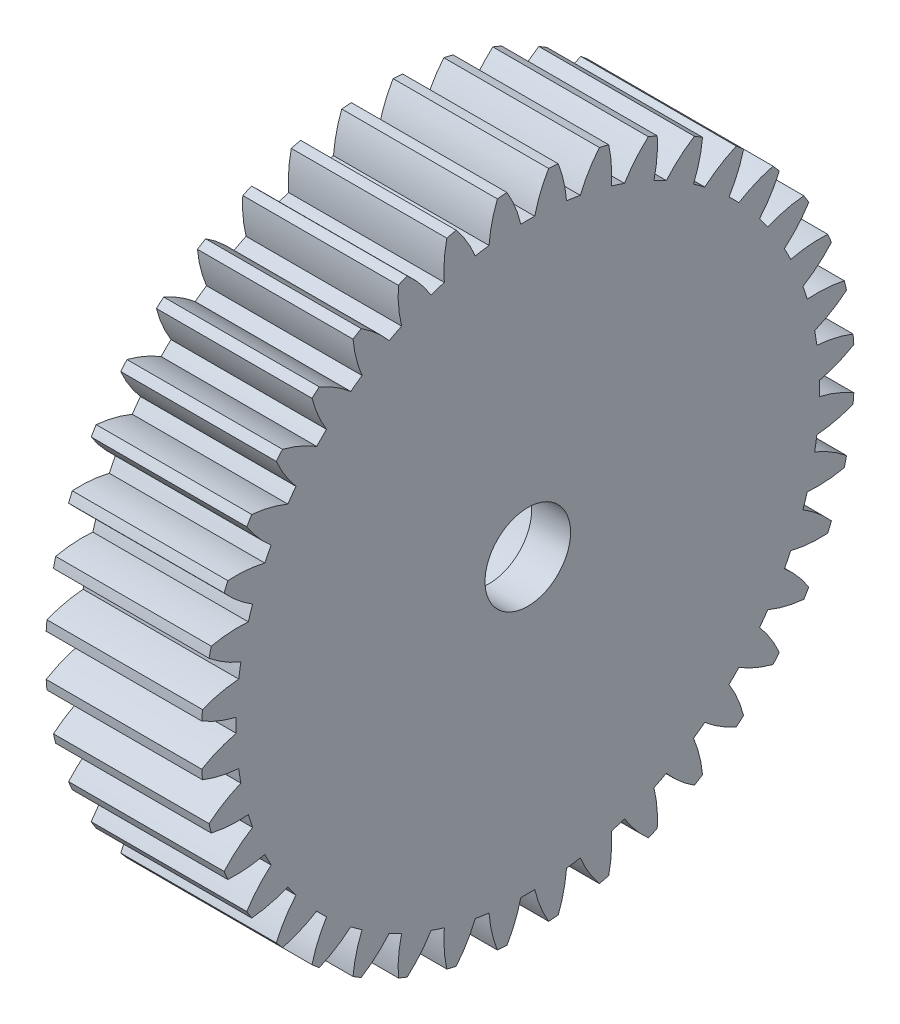
SolidWorks part; units mm, degrees
ref_plane "Front Plane" through (0, 0, 0) normal (0, 0, 1) x (1, 0, 0)
ref_plane "Top Plane" through (0, 0, 0) normal (0, 1, 0) x (1, 0, 0)
ref_plane "Right Plane" through (0, 0, 0) normal (1, 0, 0) x (0, 0, -1)
ref_plane "Plane1" through (-1.595, 0, 0) normal (1, 0, 0) x (0, 0, -1)
sketch "Sketch1" plane through (-1.595, 0, 0) normal (1, 0, 0) x (0, 0, -1)
  circle B0 centre (0, 0) radius 0.4
  arc B1 (-8.3829, 0.5357) -> (-7.4969, 0.179) centre (-6.7581, 3.2926) ccw
  arc B2 (-7.4969, 0.179) -> (-7.4969, -0.179) centre (0, 0) ccw
  arc B3 (-7.4969, -0.179) -> (-8.3829, -0.5357) centre (-6.7581, -3.2926) ccw
  arc B4 (-8.3829, -0.5357) -> (-8.3635, -0.7822) centre (0, 0) ccw
  arc B5 (-8.3635, -0.7822) -> (-7.4326, -0.996) centre (-7.19, 2.1948) ccw
  arc B6 (-7.4326, -0.996) -> (-7.3766, -1.3496) centre (0, 0) ccw
  arc B7 (-7.3766, -1.3496) -> (-8.1959, -1.8405) centre (-6.1599, -4.3092) ccw
  arc B8 (-8.1959, -1.8405) -> (-8.1382, -2.081) centre (0, 0) ccw
  arc B9 (-8.1382, -2.081) -> (-7.1853, -2.1464) centre (-7.4448, 1.043) ccw
  arc B10 (-7.1853, -2.1464) -> (-7.0746, -2.4869) centre (0, 0) ccw
  arc B11 (-7.0746, -2.4869) -> (-7.8071, -3.1) centre (-5.4099, -5.2198) ccw
  arc B12 (-7.8071, -3.1) -> (-7.7124, -3.3284) centre (0, 0) ccw
  arc B13 (-7.7124, -3.3284) -> (-6.761, -3.244) centre (-7.5163, -0.1344) ccw
  arc B14 (-6.761, -3.244) -> (-6.5985, -3.563) centre (0, 0) ccw
  arc B15 (-6.5985, -3.563) -> (-7.226, -4.2831) centre (-4.5268, -6.0018) ccw
  arc B16 (-7.226, -4.2831) -> (-7.0968, -4.4939) centre (0, 0) ccw
  arc B17 (-7.0968, -4.4939) -> (-6.1703, -4.2617) centre (-7.4028, -1.3086) ccw
  arc B18 (-6.1703, -4.2617) -> (-5.9599, -4.5514) centre (0, 0) ccw
  arc B19 (-5.9599, -4.5514) -> (-6.467, -5.3608) centre (-3.5321, -6.6361) ccw
  arc B20 (-6.467, -5.3608) -> (-6.3064, -5.5488) centre (0, 0) ccw
  arc B21 (-6.3064, -5.5488) -> (-5.4277, -5.1745) centre (-7.1069, -2.4505) ccw
  arc B22 (-5.4277, -5.1745) -> (-5.1745, -5.4277) centre (0, 0) ccw
  arc B23 (-5.1745, -5.4277) -> (-5.5488, -6.3064) centre (-2.4505, -7.1069) ccw
  arc B24 (-5.5488, -6.3064) -> (-5.3608, -6.467) centre (0, 0) ccw
  arc B25 (-5.3608, -6.467) -> (-4.5514, -5.9599) centre (-6.6361, -3.5321) ccw
  arc B26 (-4.5514, -5.9599) -> (-4.2617, -6.1703) centre (0, 0) ccw
  arc B27 (-4.2617, -6.1703) -> (-4.4939, -7.0968) centre (-1.3086, -7.4028) ccw
  arc B28 (-4.4939, -7.0968) -> (-4.2831, -7.226) centre (0, 0) ccw
  arc B29 (-4.2831, -7.226) -> (-3.563, -6.5985) centre (-6.0018, -4.5268) ccw
  arc B30 (-3.563, -6.5985) -> (-3.244, -6.761) centre (0, 0) ccw
  arc B31 (-3.244, -6.761) -> (-3.3284, -7.7124) centre (-0.1344, -7.5163) ccw
  arc B32 (-3.3284, -7.7124) -> (-3.1, -7.8071) centre (0, 0) ccw
  arc B33 (-3.1, -7.8071) -> (-2.4869, -7.0746) centre (-5.2198, -5.4099) ccw
  arc B34 (-2.4869, -7.0746) -> (-2.1464, -7.1853) centre (0, 0) ccw
  arc B35 (-2.1464, -7.1853) -> (-2.081, -8.1382) centre (1.043, -7.4448) ccw
  arc B36 (-2.081, -8.1382) -> (-1.8405, -8.1959) centre (0, 0) ccw
  arc B37 (-1.8405, -8.1959) -> (-1.3496, -7.3766) centre (-4.3092, -6.1599) ccw
  arc B38 (-1.3496, -7.3766) -> (-0.996, -7.4326) centre (0, 0) ccw
  arc B39 (-0.996, -7.4326) -> (-0.7822, -8.3635) centre (2.1948, -7.19) ccw
  arc B40 (-0.7822, -8.3635) -> (-0.5357, -8.3829) centre (0, 0) ccw
  arc B41 (-0.5357, -8.3829) -> (-0.179, -7.4969) centre (-3.2926, -6.7581) ccw
  arc B42 (-0.179, -7.4969) -> (0.179, -7.4969) centre (0, 0) ccw
  arc B43 (0.179, -7.4969) -> (0.5357, -8.3829) centre (3.2926, -6.7581) ccw
  arc B44 (0.5357, -8.3829) -> (0.7822, -8.3635) centre (0, 0) ccw
  arc B45 (0.7822, -8.3635) -> (0.996, -7.4326) centre (-2.1948, -7.19) ccw
  arc B46 (0.996, -7.4326) -> (1.3496, -7.3766) centre (0, 0) ccw
  arc B47 (1.3496, -7.3766) -> (1.8405, -8.1959) centre (4.3092, -6.1599) ccw
  arc B48 (1.8405, -8.1959) -> (2.081, -8.1382) centre (0, 0) ccw
  arc B49 (2.081, -8.1382) -> (2.1464, -7.1853) centre (-1.043, -7.4448) ccw
  arc B50 (2.1464, -7.1853) -> (2.4869, -7.0746) centre (0, 0) ccw
  arc B51 (2.4869, -7.0746) -> (3.1, -7.8071) centre (5.2198, -5.4099) ccw
  arc B52 (3.1, -7.8071) -> (3.3284, -7.7124) centre (0, 0) ccw
  arc B53 (3.3284, -7.7124) -> (3.244, -6.761) centre (0.1344, -7.5163) ccw
  arc B54 (3.244, -6.761) -> (3.563, -6.5985) centre (0, 0) ccw
  arc B55 (3.563, -6.5985) -> (4.2831, -7.226) centre (6.0018, -4.5268) ccw
  arc B56 (4.2831, -7.226) -> (4.4939, -7.0968) centre (0, 0) ccw
  arc B57 (4.4939, -7.0968) -> (4.2617, -6.1703) centre (1.3086, -7.4028) ccw
  arc B58 (4.2617, -6.1703) -> (4.5514, -5.9599) centre (0, 0) ccw
  arc B59 (4.5514, -5.9599) -> (5.3608, -6.467) centre (6.6361, -3.5321) ccw
  arc B60 (5.3608, -6.467) -> (5.5488, -6.3064) centre (0, 0) ccw
  arc B61 (5.5488, -6.3064) -> (5.1745, -5.4277) centre (2.4505, -7.1069) ccw
  arc B62 (5.1745, -5.4277) -> (5.4277, -5.1745) centre (0, 0) ccw
  arc B63 (5.4277, -5.1745) -> (6.3064, -5.5488) centre (7.1069, -2.4505) ccw
  arc B64 (6.3064, -5.5488) -> (6.467, -5.3608) centre (0, 0) ccw
  arc B65 (6.467, -5.3608) -> (5.9599, -4.5514) centre (3.5321, -6.6361) ccw
  arc B66 (5.9599, -4.5514) -> (6.1703, -4.2617) centre (0, 0) ccw
  arc B67 (6.1703, -4.2617) -> (7.0968, -4.4939) centre (7.4028, -1.3086) ccw
  arc B68 (7.0968, -4.4939) -> (7.226, -4.2831) centre (0, 0) ccw
  arc B69 (7.226, -4.2831) -> (6.5985, -3.563) centre (4.5268, -6.0018) ccw
  arc B70 (6.5985, -3.563) -> (6.761, -3.244) centre (0, 0) ccw
  arc B71 (6.761, -3.244) -> (7.7124, -3.3284) centre (7.5163, -0.1344) ccw
  arc B72 (7.7124, -3.3284) -> (7.8071, -3.1) centre (0, 0) ccw
  arc B73 (7.8071, -3.1) -> (7.0746, -2.4869) centre (5.4099, -5.2198) ccw
  arc B74 (7.0746, -2.4869) -> (7.1853, -2.1464) centre (0, 0) ccw
  arc B75 (7.1853, -2.1464) -> (8.1382, -2.081) centre (7.4448, 1.043) ccw
  arc B76 (8.1382, -2.081) -> (8.1959, -1.8405) centre (0, 0) ccw
  arc B77 (8.1959, -1.8405) -> (7.3766, -1.3496) centre (6.1599, -4.3092) ccw
  arc B78 (7.3766, -1.3496) -> (7.4326, -0.996) centre (0, 0) ccw
  arc B79 (7.4326, -0.996) -> (8.3635, -0.7822) centre (7.19, 2.1948) ccw
  arc B80 (8.3635, -0.7822) -> (8.3829, -0.5357) centre (0, 0) ccw
  arc B81 (8.3829, -0.5357) -> (7.4969, -0.179) centre (6.7581, -3.2926) ccw
  arc B82 (7.4969, -0.179) -> (7.4969, 0.179) centre (0, 0) ccw
  arc B83 (7.4969, 0.179) -> (8.3829, 0.5357) centre (6.7581, 3.2926) ccw
  arc B84 (8.3829, 0.5357) -> (8.3635, 0.7822) centre (0, 0) ccw
  arc B85 (8.3635, 0.7822) -> (7.4326, 0.996) centre (7.19, -2.1948) ccw
  arc B86 (7.4326, 0.996) -> (7.3766, 1.3496) centre (0, 0) ccw
  arc B87 (7.3766, 1.3496) -> (8.1959, 1.8405) centre (6.1599, 4.3092) ccw
  arc B88 (8.1959, 1.8405) -> (8.1382, 2.081) centre (0, 0) ccw
  arc B89 (8.1382, 2.081) -> (7.1853, 2.1464) centre (7.4448, -1.043) ccw
  arc B90 (7.1853, 2.1464) -> (7.0746, 2.4869) centre (0, 0) ccw
  arc B91 (7.0746, 2.4869) -> (7.8071, 3.1) centre (5.4099, 5.2198) ccw
  arc B92 (7.8071, 3.1) -> (7.7124, 3.3284) centre (0, 0) ccw
  arc B93 (7.7124, 3.3284) -> (6.761, 3.244) centre (7.5163, 0.1344) ccw
  arc B94 (6.761, 3.244) -> (6.5985, 3.563) centre (0, 0) ccw
  arc B95 (6.5985, 3.563) -> (7.226, 4.2831) centre (4.5268, 6.0018) ccw
  arc B96 (7.226, 4.2831) -> (7.0968, 4.4939) centre (0, 0) ccw
  arc B97 (7.0968, 4.4939) -> (6.1703, 4.2617) centre (7.4028, 1.3086) ccw
  arc B98 (6.1703, 4.2617) -> (5.9599, 4.5514) centre (0, 0) ccw
  arc B99 (5.9599, 4.5514) -> (6.467, 5.3608) centre (3.5321, 6.6361) ccw
  arc B100 (6.467, 5.3608) -> (6.3064, 5.5488) centre (0, 0) ccw
  arc B101 (6.3064, 5.5488) -> (5.4277, 5.1745) centre (7.1069, 2.4505) ccw
  arc B102 (5.4277, 5.1745) -> (5.1745, 5.4277) centre (0, 0) ccw
  arc B103 (5.1745, 5.4277) -> (5.5488, 6.3064) centre (2.4505, 7.1069) ccw
  arc B104 (5.5488, 6.3064) -> (5.3608, 6.467) centre (0, 0) ccw
  arc B105 (5.3608, 6.467) -> (4.5514, 5.9599) centre (6.6361, 3.5321) ccw
  arc B106 (4.5514, 5.9599) -> (4.2617, 6.1703) centre (0, 0) ccw
  arc B107 (4.2617, 6.1703) -> (4.4939, 7.0968) centre (1.3086, 7.4028) ccw
  arc B108 (4.4939, 7.0968) -> (4.2831, 7.226) centre (0, 0) ccw
  arc B109 (4.2831, 7.226) -> (3.563, 6.5985) centre (6.0018, 4.5268) ccw
  arc B110 (3.563, 6.5985) -> (3.244, 6.761) centre (0, 0) ccw
  arc B111 (3.244, 6.761) -> (3.3284, 7.7124) centre (0.1344, 7.5163) ccw
  arc B112 (3.3284, 7.7124) -> (3.1, 7.8071) centre (0, 0) ccw
  arc B113 (3.1, 7.8071) -> (2.4869, 7.0746) centre (5.2198, 5.4099) ccw
  arc B114 (2.4869, 7.0746) -> (2.1464, 7.1853) centre (0, 0) ccw
  arc B115 (2.1464, 7.1853) -> (2.081, 8.1382) centre (-1.043, 7.4448) ccw
  arc B116 (2.081, 8.1382) -> (1.8405, 8.1959) centre (0, 0) ccw
  arc B117 (1.8405, 8.1959) -> (1.3496, 7.3766) centre (4.3092, 6.1599) ccw
  arc B118 (1.3496, 7.3766) -> (0.996, 7.4326) centre (0, 0) ccw
  arc B119 (0.996, 7.4326) -> (0.7822, 8.3635) centre (-2.1948, 7.19) ccw
  arc B120 (0.7822, 8.3635) -> (0.5357, 8.3829) centre (0, 0) ccw
  arc B121 (0.5357, 8.3829) -> (0.179, 7.4969) centre (3.2926, 6.7581) ccw
  arc B122 (0.179, 7.4969) -> (-0.179, 7.4969) centre (0, 0) ccw
  arc B123 (-0.179, 7.4969) -> (-0.5357, 8.3829) centre (-3.2926, 6.7581) ccw
  arc B124 (-0.5357, 8.3829) -> (-0.7822, 8.3635) centre (0, 0) ccw
  arc B125 (-0.7822, 8.3635) -> (-0.996, 7.4326) centre (2.1948, 7.19) ccw
  arc B126 (-0.996, 7.4326) -> (-1.3496, 7.3766) centre (0, 0) ccw
  arc B127 (-1.3496, 7.3766) -> (-1.8405, 8.1959) centre (-4.3092, 6.1599) ccw
  arc B128 (-1.8405, 8.1959) -> (-2.081, 8.1382) centre (0, 0) ccw
  arc B129 (-2.081, 8.1382) -> (-2.1464, 7.1853) centre (1.043, 7.4448) ccw
  arc B130 (-2.1464, 7.1853) -> (-2.4869, 7.0746) centre (0, 0) ccw
  arc B131 (-2.4869, 7.0746) -> (-3.1, 7.8071) centre (-5.2198, 5.4099) ccw
  arc B132 (-3.1, 7.8071) -> (-3.3284, 7.7124) centre (0, 0) ccw
  arc B133 (-3.3284, 7.7124) -> (-3.244, 6.761) centre (-0.1344, 7.5163) ccw
  arc B134 (-3.244, 6.761) -> (-3.563, 6.5985) centre (0, 0) ccw
  arc B135 (-3.563, 6.5985) -> (-4.2831, 7.226) centre (-6.0018, 4.5268) ccw
  arc B136 (-4.2831, 7.226) -> (-4.4939, 7.0968) centre (0, 0) ccw
  arc B137 (-4.4939, 7.0968) -> (-4.2617, 6.1703) centre (-1.3086, 7.4028) ccw
  arc B138 (-4.2617, 6.1703) -> (-4.5514, 5.9599) centre (0, 0) ccw
  arc B139 (-4.5514, 5.9599) -> (-5.3608, 6.467) centre (-6.6361, 3.5321) ccw
  arc B140 (-5.3608, 6.467) -> (-5.5488, 6.3064) centre (0, 0) ccw
  arc B141 (-5.5488, 6.3064) -> (-5.1745, 5.4277) centre (-2.4505, 7.1069) ccw
  arc B142 (-5.1745, 5.4277) -> (-5.4277, 5.1745) centre (0, 0) ccw
  arc B143 (-5.4277, 5.1745) -> (-6.3064, 5.5488) centre (-7.1069, 2.4505) ccw
  arc B144 (-6.3064, 5.5488) -> (-6.467, 5.3608) centre (0, 0) ccw
  arc B145 (-6.467, 5.3608) -> (-5.9599, 4.5514) centre (-3.5321, 6.6361) ccw
  arc B146 (-5.9599, 4.5514) -> (-6.1703, 4.2617) centre (0, 0) ccw
  arc B147 (-6.1703, 4.2617) -> (-7.0968, 4.4939) centre (-7.4028, 1.3086) ccw
  arc B148 (-7.0968, 4.4939) -> (-7.226, 4.2831) centre (0, 0) ccw
  arc B149 (-7.226, 4.2831) -> (-6.5985, 3.563) centre (-4.5268, 6.0018) ccw
  arc B150 (-6.5985, 3.563) -> (-6.761, 3.244) centre (0, 0) ccw
  arc B151 (-6.761, 3.244) -> (-7.7124, 3.3284) centre (-7.5163, 0.1344) ccw
  arc B152 (-7.7124, 3.3284) -> (-7.8071, 3.1) centre (0, 0) ccw
  arc B153 (-7.8071, 3.1) -> (-7.0746, 2.4869) centre (-5.4099, 5.2198) ccw
  arc B154 (-7.0746, 2.4869) -> (-7.1853, 2.1464) centre (0, 0) ccw
  arc B155 (-7.1853, 2.1464) -> (-8.1382, 2.081) centre (-7.4448, -1.043) ccw
  arc B156 (-8.1382, 2.081) -> (-8.1959, 1.8405) centre (0, 0) ccw
  arc B157 (-8.1959, 1.8405) -> (-7.3766, 1.3496) centre (-6.1599, 4.3092) ccw
  arc B158 (-7.3766, 1.3496) -> (-7.4326, 0.996) centre (0, 0) ccw
  arc B159 (-7.4326, 0.996) -> (-8.3635, 0.7822) centre (-7.19, -2.1948) ccw
  arc B160 (-8.3635, 0.7822) -> (-8.3829, 0.5357) centre (0, 0) ccw
sketch_block_instance "Block2-1"
sketch_block "Block2"
extrude "Boss-Extrude1" add sketch "Sketch1" against normal blind 3
sketch "Sketch4" plane through (-1.595, 0, 0) normal (1, 0, 0) x (0, 0, -1)
  circle A0 centre (0, 0) radius 2.55
  dimension "D1" = 5.1
extrude "Cut-Extrude2" cut sketch "Sketch4" against normal through all
sketch "Sketch5" plane through (-1.595, 0, 0) normal (1, 0, 0) x (0, 0, -1)
  arc A160 (-8.3635, 0.7822) -> (-8.3829, 0.5357) centre (0, 0) ccw
  arc A161 (-8.3829, 0.5357) -> (-7.4969, 0.179) centre (-6.7581, 3.2926) ccw
  arc A162 (-7.4969, 0.179) -> (-7.4969, -0.179) centre (0, 0) ccw
  arc A163 (-7.4969, -0.179) -> (-8.3829, -0.5357) centre (-6.7581, -3.2926) ccw
  arc A164 (-8.3829, -0.5357) -> (-8.3635, -0.7822) centre (0, 0) ccw
  arc A165 (-8.3635, -0.7822) -> (-7.4326, -0.996) centre (-7.19, 2.1948) ccw
  arc A166 (-7.4326, -0.996) -> (-7.3766, -1.3496) centre (0, 0) ccw
  arc A167 (-7.3766, -1.3496) -> (-8.1959, -1.8405) centre (-6.1599, -4.3092) ccw
  arc A168 (-8.1959, -1.8405) -> (-8.1382, -2.081) centre (0, 0) ccw
  arc A169 (-8.1382, -2.081) -> (-7.1853, -2.1464) centre (-7.4448, 1.043) ccw
  arc A170 (-7.1853, -2.1464) -> (-7.0746, -2.4869) centre (0, 0) ccw
  arc A171 (-7.0746, -2.4869) -> (-7.8071, -3.1) centre (-5.4099, -5.2198) ccw
  arc A172 (-7.8071, -3.1) -> (-7.7124, -3.3284) centre (0, 0) ccw
  arc A173 (-7.7124, -3.3284) -> (-6.761, -3.244) centre (-7.5163, -0.1344) ccw
  arc A174 (-6.761, -3.244) -> (-6.5985, -3.563) centre (0, 0) ccw
  arc A175 (-6.5985, -3.563) -> (-7.226, -4.2831) centre (-4.5268, -6.0018) ccw
  arc A176 (-7.226, -4.2831) -> (-7.0968, -4.4939) centre (0, 0) ccw
  arc A177 (-7.0968, -4.4939) -> (-6.1703, -4.2617) centre (-7.4028, -1.3086) ccw
  arc A178 (-6.1703, -4.2617) -> (-5.9599, -4.5514) centre (0, 0) ccw
  arc A179 (-5.9599, -4.5514) -> (-6.467, -5.3608) centre (-3.5321, -6.6361) ccw
  arc A180 (-6.467, -5.3608) -> (-6.3064, -5.5488) centre (0, 0) ccw
  arc A181 (-6.3064, -5.5488) -> (-5.4277, -5.1745) centre (-7.1069, -2.4505) ccw
  arc A182 (-5.4277, -5.1745) -> (-5.1745, -5.4277) centre (0, 0) ccw
  arc A183 (-5.1745, -5.4277) -> (-5.5488, -6.3064) centre (-2.4505, -7.1069) ccw
  arc A184 (-5.5488, -6.3064) -> (-5.3608, -6.467) centre (0, 0) ccw
  arc A185 (-5.3608, -6.467) -> (-4.5514, -5.9599) centre (-6.6361, -3.5321) ccw
  arc A186 (-4.5514, -5.9599) -> (-4.2617, -6.1703) centre (0, 0) ccw
  arc A187 (-4.2617, -6.1703) -> (-4.4939, -7.0968) centre (-1.3086, -7.4028) ccw
  arc A188 (-4.4939, -7.0968) -> (-4.2831, -7.226) centre (0, 0) ccw
  arc A189 (-4.2831, -7.226) -> (-3.563, -6.5985) centre (-6.0018, -4.5268) ccw
  arc A190 (-3.563, -6.5985) -> (-3.244, -6.761) centre (0, 0) ccw
  arc A191 (-3.244, -6.761) -> (-3.3284, -7.7124) centre (-0.1344, -7.5163) ccw
  arc A192 (-3.3284, -7.7124) -> (-3.1, -7.8071) centre (0, 0) ccw
  arc A193 (-3.1, -7.8071) -> (-2.4869, -7.0746) centre (-5.2198, -5.4099) ccw
  arc A194 (-2.4869, -7.0746) -> (-2.1464, -7.1853) centre (0, 0) ccw
  arc A195 (-2.1464, -7.1853) -> (-2.081, -8.1382) centre (1.043, -7.4448) ccw
  arc A196 (-2.081, -8.1382) -> (-1.8405, -8.1959) centre (0, 0) ccw
  arc A197 (-1.8405, -8.1959) -> (-1.3496, -7.3766) centre (-4.3092, -6.1599) ccw
  arc A198 (-1.3496, -7.3766) -> (-0.996, -7.4326) centre (0, 0) ccw
  arc A199 (-0.996, -7.4326) -> (-0.7822, -8.3635) centre (2.1948, -7.19) ccw
  arc A200 (-0.7822, -8.3635) -> (-0.5357, -8.3829) centre (0, 0) ccw
  arc A201 (-0.5357, -8.3829) -> (-0.179, -7.4969) centre (-3.2926, -6.7581) ccw
  arc A202 (-0.179, -7.4969) -> (0.179, -7.4969) centre (0, 0) ccw
  arc A203 (0.179, -7.4969) -> (0.5357, -8.3829) centre (3.2926, -6.7581) ccw
  arc A204 (0.5357, -8.3829) -> (0.7822, -8.3635) centre (0, 0) ccw
  arc A205 (0.7822, -8.3635) -> (0.996, -7.4326) centre (-2.1948, -7.19) ccw
  arc A206 (0.996, -7.4326) -> (1.3496, -7.3766) centre (0, 0) ccw
  arc A207 (1.3496, -7.3766) -> (1.8405, -8.1959) centre (4.3092, -6.1599) ccw
  arc A208 (1.8405, -8.1959) -> (2.081, -8.1382) centre (0, 0) ccw
  arc A209 (2.081, -8.1382) -> (2.1464, -7.1853) centre (-1.043, -7.4448) ccw
  arc A210 (2.1464, -7.1853) -> (2.4869, -7.0746) centre (0, 0) ccw
  arc A211 (2.4869, -7.0746) -> (3.1, -7.8071) centre (5.2198, -5.4099) ccw
  arc A212 (3.1, -7.8071) -> (3.3284, -7.7124) centre (0, 0) ccw
  arc A213 (3.3284, -7.7124) -> (3.244, -6.761) centre (0.1344, -7.5163) ccw
  arc A214 (3.244, -6.761) -> (3.563, -6.5985) centre (0, 0) ccw
  arc A215 (3.563, -6.5985) -> (4.2831, -7.226) centre (6.0018, -4.5268) ccw
  arc A216 (4.2831, -7.226) -> (4.4939, -7.0968) centre (0, 0) ccw
  arc A217 (4.4939, -7.0968) -> (4.2617, -6.1703) centre (1.3086, -7.4028) ccw
  arc A218 (4.2617, -6.1703) -> (4.5514, -5.9599) centre (0, 0) ccw
  arc A219 (4.5514, -5.9599) -> (5.3608, -6.467) centre (6.6361, -3.5321) ccw
  arc A220 (5.3608, -6.467) -> (5.5488, -6.3064) centre (0, 0) ccw
  arc A221 (5.5488, -6.3064) -> (5.1745, -5.4277) centre (2.4505, -7.1069) ccw
  arc A222 (5.1745, -5.4277) -> (5.4277, -5.1745) centre (0, 0) ccw
  arc A223 (5.4277, -5.1745) -> (6.3064, -5.5488) centre (7.1069, -2.4505) ccw
  arc A224 (6.3064, -5.5488) -> (6.467, -5.3608) centre (0, 0) ccw
  arc A225 (6.467, -5.3608) -> (5.9599, -4.5514) centre (3.5321, -6.6361) ccw
  arc A226 (5.9599, -4.5514) -> (6.1703, -4.2617) centre (0, 0) ccw
  arc A227 (6.1703, -4.2617) -> (7.0968, -4.4939) centre (7.4028, -1.3086) ccw
  arc A228 (7.0968, -4.4939) -> (7.226, -4.2831) centre (0, 0) ccw
  arc A229 (7.226, -4.2831) -> (6.5985, -3.563) centre (4.5268, -6.0018) ccw
  arc A230 (6.5985, -3.563) -> (6.761, -3.244) centre (0, 0) ccw
  arc A231 (6.761, -3.244) -> (7.7124, -3.3284) centre (7.5163, -0.1344) ccw
  arc A232 (7.7124, -3.3284) -> (7.8071, -3.1) centre (0, 0) ccw
  arc A233 (7.8071, -3.1) -> (7.0746, -2.4869) centre (5.4099, -5.2198) ccw
  arc A234 (7.0746, -2.4869) -> (7.1853, -2.1464) centre (0, 0) ccw
  arc A235 (7.1853, -2.1464) -> (8.1382, -2.081) centre (7.4448, 1.043) ccw
  arc A236 (8.1382, -2.081) -> (8.1959, -1.8405) centre (0, 0) ccw
  arc A237 (8.1959, -1.8405) -> (7.3766, -1.3496) centre (6.1599, -4.3092) ccw
  arc A238 (7.3766, -1.3496) -> (7.4326, -0.996) centre (0, 0) ccw
  arc A239 (7.4326, -0.996) -> (8.3635, -0.7822) centre (7.19, 2.1948) ccw
  arc A240 (8.3635, -0.7822) -> (8.3829, -0.5357) centre (0, 0) ccw
  arc A241 (8.3829, -0.5357) -> (7.4969, -0.179) centre (6.7581, -3.2926) ccw
  arc A242 (7.4969, -0.179) -> (7.4969, 0.179) centre (0, 0) ccw
  arc A243 (7.4969, 0.179) -> (8.3829, 0.5357) centre (6.7581, 3.2926) ccw
  arc A244 (8.3829, 0.5357) -> (8.3635, 0.7822) centre (0, 0) ccw
  arc A245 (8.3635, 0.7822) -> (7.4326, 0.996) centre (7.19, -2.1948) ccw
  arc A246 (7.4326, 0.996) -> (7.3766, 1.3496) centre (0, 0) ccw
  arc A247 (7.3766, 1.3496) -> (8.1959, 1.8405) centre (6.1599, 4.3092) ccw
  arc A248 (8.1959, 1.8405) -> (8.1382, 2.081) centre (0, 0) ccw
  arc A249 (8.1382, 2.081) -> (7.1853, 2.1464) centre (7.4448, -1.043) ccw
  arc A250 (7.1853, 2.1464) -> (7.0746, 2.4869) centre (0, 0) ccw
  arc A251 (7.0746, 2.4869) -> (7.8071, 3.1) centre (5.4099, 5.2198) ccw
  arc A252 (7.8071, 3.1) -> (7.7124, 3.3284) centre (0, 0) ccw
  arc A253 (7.7124, 3.3284) -> (6.761, 3.244) centre (7.5163, 0.1344) ccw
  arc A254 (6.761, 3.244) -> (6.5985, 3.563) centre (0, 0) ccw
  arc A255 (6.5985, 3.563) -> (7.226, 4.2831) centre (4.5268, 6.0018) ccw
  arc A256 (7.226, 4.2831) -> (7.0968, 4.4939) centre (0, 0) ccw
  arc A257 (7.0968, 4.4939) -> (6.1703, 4.2617) centre (7.4028, 1.3086) ccw
  arc A258 (6.1703, 4.2617) -> (5.9599, 4.5514) centre (0, 0) ccw
  arc A259 (5.9599, 4.5514) -> (6.467, 5.3608) centre (3.5321, 6.6361) ccw
  arc A260 (6.467, 5.3608) -> (6.3064, 5.5488) centre (0, 0) ccw
  arc A261 (6.3064, 5.5488) -> (5.4277, 5.1745) centre (7.1069, 2.4505) ccw
  arc A262 (5.4277, 5.1745) -> (5.1745, 5.4277) centre (0, 0) ccw
  arc A263 (5.1745, 5.4277) -> (5.5488, 6.3064) centre (2.4505, 7.1069) ccw
  arc A264 (5.5488, 6.3064) -> (5.3608, 6.467) centre (0, 0) ccw
  arc A265 (5.3608, 6.467) -> (4.5514, 5.9599) centre (6.6361, 3.5321) ccw
  arc A266 (4.5514, 5.9599) -> (4.2617, 6.1703) centre (0, 0) ccw
  arc A267 (4.2617, 6.1703) -> (4.4939, 7.0968) centre (1.3086, 7.4028) ccw
  arc A268 (4.4939, 7.0968) -> (4.2831, 7.226) centre (0, 0) ccw
  arc A269 (4.2831, 7.226) -> (3.563, 6.5985) centre (6.0018, 4.5268) ccw
  arc A270 (3.563, 6.5985) -> (3.244, 6.761) centre (0, 0) ccw
  arc A271 (3.244, 6.761) -> (3.3284, 7.7124) centre (0.1344, 7.5163) ccw
  arc A272 (3.3284, 7.7124) -> (3.1, 7.8071) centre (0, 0) ccw
  arc A273 (3.1, 7.8071) -> (2.4869, 7.0746) centre (5.2198, 5.4099) ccw
  arc A274 (2.4869, 7.0746) -> (2.1464, 7.1853) centre (0, 0) ccw
  arc A275 (2.1464, 7.1853) -> (2.081, 8.1382) centre (-1.043, 7.4448) ccw
  arc A276 (2.081, 8.1382) -> (1.8405, 8.1959) centre (0, 0) ccw
  arc A277 (1.8405, 8.1959) -> (1.3496, 7.3766) centre (4.3092, 6.1599) ccw
  arc A278 (1.3496, 7.3766) -> (0.996, 7.4326) centre (0, 0) ccw
  arc A279 (0.996, 7.4326) -> (0.7822, 8.3635) centre (-2.1948, 7.19) ccw
  arc A280 (0.7822, 8.3635) -> (0.5357, 8.3829) centre (0, 0) ccw
  arc A281 (0.5357, 8.3829) -> (0.179, 7.4969) centre (3.2926, 6.7581) ccw
  arc A282 (0.179, 7.4969) -> (-0.179, 7.4969) centre (0, 0) ccw
  arc A283 (-0.179, 7.4969) -> (-0.5357, 8.3829) centre (-3.2926, 6.7581) ccw
  arc A284 (-0.5357, 8.3829) -> (-0.7822, 8.3635) centre (0, 0) ccw
  arc A285 (-0.7822, 8.3635) -> (-0.996, 7.4326) centre (2.1948, 7.19) ccw
  arc A286 (-0.996, 7.4326) -> (-1.3496, 7.3766) centre (0, 0) ccw
  arc A287 (-1.3496, 7.3766) -> (-1.8405, 8.1959) centre (-4.3092, 6.1599) ccw
  arc A288 (-1.8405, 8.1959) -> (-2.081, 8.1382) centre (0, 0) ccw
  arc A289 (-2.081, 8.1382) -> (-2.1464, 7.1853) centre (1.043, 7.4448) ccw
  arc A290 (-2.1464, 7.1853) -> (-2.4869, 7.0746) centre (0, 0) ccw
  arc A291 (-2.4869, 7.0746) -> (-3.1, 7.8071) centre (-5.2198, 5.4099) ccw
  arc A292 (-3.1, 7.8071) -> (-3.3284, 7.7124) centre (0, 0) ccw
  arc A293 (-3.3284, 7.7124) -> (-3.244, 6.761) centre (-0.1344, 7.5163) ccw
  arc A294 (-3.244, 6.761) -> (-3.563, 6.5985) centre (0, 0) ccw
  arc A295 (-3.563, 6.5985) -> (-4.2831, 7.226) centre (-6.0018, 4.5268) ccw
  arc A296 (-4.2831, 7.226) -> (-4.4939, 7.0968) centre (0, 0) ccw
  arc A297 (-4.4939, 7.0968) -> (-4.2617, 6.1703) centre (-1.3086, 7.4028) ccw
  arc A298 (-4.2617, 6.1703) -> (-4.5514, 5.9599) centre (0, 0) ccw
  arc A299 (-4.5514, 5.9599) -> (-5.3608, 6.467) centre (-6.6361, 3.5321) ccw
  arc A300 (-5.3608, 6.467) -> (-5.5488, 6.3064) centre (0, 0) ccw
  arc A301 (-5.5488, 6.3064) -> (-5.1745, 5.4277) centre (-2.4505, 7.1069) ccw
  arc A302 (-5.1745, 5.4277) -> (-5.4277, 5.1745) centre (0, 0) ccw
  arc A303 (-5.4277, 5.1745) -> (-6.3064, 5.5488) centre (-7.1069, 2.4505) ccw
  arc A304 (-6.3064, 5.5488) -> (-6.467, 5.3608) centre (0, 0) ccw
  arc A305 (-6.467, 5.3608) -> (-5.9599, 4.5514) centre (-3.5321, 6.6361) ccw
  arc A306 (-5.9599, 4.5514) -> (-6.1703, 4.2617) centre (0, 0) ccw
  arc A307 (-6.1703, 4.2617) -> (-7.0968, 4.4939) centre (-7.4028, 1.3086) ccw
  arc A308 (-7.0968, 4.4939) -> (-7.226, 4.2831) centre (0, 0) ccw
  arc A309 (-7.226, 4.2831) -> (-6.5985, 3.563) centre (-4.5268, 6.0018) ccw
  arc A310 (-6.5985, 3.563) -> (-6.761, 3.244) centre (0, 0) ccw
  arc A311 (-6.761, 3.244) -> (-7.7124, 3.3284) centre (-7.5163, 0.1344) ccw
  arc A312 (-7.7124, 3.3284) -> (-7.8071, 3.1) centre (0, 0) ccw
  arc A313 (-7.8071, 3.1) -> (-7.0746, 2.4869) centre (-5.4099, 5.2198) ccw
  arc A314 (-7.0746, 2.4869) -> (-7.1853, 2.1464) centre (0, 0) ccw
  arc A315 (-7.1853, 2.1464) -> (-8.1382, 2.081) centre (-7.4448, -1.043) ccw
  arc A316 (-8.1382, 2.081) -> (-8.1959, 1.8405) centre (0, 0) ccw
  arc A317 (-8.1959, 1.8405) -> (-7.3766, 1.3496) centre (-6.1599, 4.3092) ccw
  arc A318 (-7.3766, 1.3496) -> (-7.4326, 0.996) centre (0, 0) ccw
  arc A319 (-7.4326, 0.996) -> (-8.3635, 0.7822) centre (-7.19, -2.1948) ccw
  arc A320 (-8.3635, 0.7822) -> (-8.3829, 0.5357) centre (0, 0) ccw
  arc A321 (-8.3829, 0.5357) -> (-7.4969, 0.179) centre (-6.7581, 3.2926) ccw
  arc A322 (-7.4969, 0.179) -> (-7.4969, -0.179) centre (0, 0) ccw
  arc A323 (-7.4969, -0.179) -> (-8.3829, -0.5357) centre (-6.7581, -3.2926) ccw
  arc A324 (-8.3829, -0.5357) -> (-8.3635, -0.7822) centre (0, 0) ccw
  arc A325 (-8.3635, -0.7822) -> (-7.4326, -0.996) centre (-7.19, 2.1948) ccw
  arc A326 (-7.4326, -0.996) -> (-7.3766, -1.3496) centre (0, 0) ccw
  arc A327 (-7.3766, -1.3496) -> (-8.1959, -1.8405) centre (-6.1599, -4.3092) ccw
  arc A328 (-8.1959, -1.8405) -> (-8.1382, -2.081) centre (0, 0) ccw
  arc A329 (-8.1382, -2.081) -> (-7.1853, -2.1464) centre (-7.4448, 1.043) ccw
  arc A330 (-7.1853, -2.1464) -> (-7.0746, -2.4869) centre (0, 0) ccw
  arc A331 (-7.0746, -2.4869) -> (-7.8071, -3.1) centre (-5.4099, -5.2198) ccw
  arc A332 (-7.8071, -3.1) -> (-7.7124, -3.3284) centre (0, 0) ccw
  arc A333 (-7.7124, -3.3284) -> (-6.761, -3.244) centre (-7.5163, -0.1344) ccw
  arc A334 (-6.761, -3.244) -> (-6.5985, -3.563) centre (0, 0) ccw
  arc A335 (-6.5985, -3.563) -> (-7.226, -4.2831) centre (-4.5268, -6.0018) ccw
  arc A336 (-7.226, -4.2831) -> (-7.0968, -4.4939) centre (0, 0) ccw
  arc A337 (-7.0968, -4.4939) -> (-6.1703, -4.2617) centre (-7.4028, -1.3086) ccw
  arc A338 (-6.1703, -4.2617) -> (-5.9599, -4.5514) centre (0, 0) ccw
  arc A339 (-5.9599, -4.5514) -> (-6.467, -5.3608) centre (-3.5321, -6.6361) ccw
  arc A340 (-6.467, -5.3608) -> (-6.3064, -5.5488) centre (0, 0) ccw
  arc A341 (-6.3064, -5.5488) -> (-5.4277, -5.1745) centre (-7.1069, -2.4505) ccw
  arc A342 (-5.4277, -5.1745) -> (-5.1745, -5.4277) centre (0, 0) ccw
  arc A343 (-5.1745, -5.4277) -> (-5.5488, -6.3064) centre (-2.4505, -7.1069) ccw
  arc A344 (-5.5488, -6.3064) -> (-5.3608, -6.467) centre (0, 0) ccw
  arc A345 (-5.3608, -6.467) -> (-4.5514, -5.9599) centre (-6.6361, -3.5321) ccw
  arc A346 (-4.5514, -5.9599) -> (-4.2617, -6.1703) centre (0, 0) ccw
  arc A347 (-4.2617, -6.1703) -> (-4.4939, -7.0968) centre (-1.3086, -7.4028) ccw
  arc A348 (-4.4939, -7.0968) -> (-4.2831, -7.226) centre (0, 0) ccw
  arc A349 (-4.2831, -7.226) -> (-3.563, -6.5985) centre (-6.0018, -4.5268) ccw
  arc A350 (-3.563, -6.5985) -> (-3.244, -6.761) centre (0, 0) ccw
  arc A351 (-3.244, -6.761) -> (-3.3284, -7.7124) centre (-0.1344, -7.5163) ccw
  arc A352 (-3.3284, -7.7124) -> (-3.1, -7.8071) centre (0, 0) ccw
  arc A353 (-3.1, -7.8071) -> (-2.4869, -7.0746) centre (-5.2198, -5.4099) ccw
  arc A354 (-2.4869, -7.0746) -> (-2.1464, -7.1853) centre (0, 0) ccw
  arc A355 (-2.1464, -7.1853) -> (-2.081, -8.1382) centre (1.043, -7.4448) ccw
  arc A356 (-2.081, -8.1382) -> (-1.8405, -8.1959) centre (0, 0) ccw
  arc A357 (-1.8405, -8.1959) -> (-1.3496, -7.3766) centre (-4.3092, -6.1599) ccw
  arc A358 (-1.3496, -7.3766) -> (-0.996, -7.4326) centre (0, 0) ccw
  arc A359 (-0.996, -7.4326) -> (-0.7822, -8.3635) centre (2.1948, -7.19) ccw
  arc A360 (-0.7822, -8.3635) -> (-0.5357, -8.3829) centre (0, 0) ccw
  arc A361 (-0.5357, -8.3829) -> (-0.179, -7.4969) centre (-3.2926, -6.7581) ccw
  arc A362 (-0.179, -7.4969) -> (0.179, -7.4969) centre (0, 0) ccw
  arc A363 (0.179, -7.4969) -> (0.5357, -8.3829) centre (3.2926, -6.7581) ccw
  arc A364 (0.5357, -8.3829) -> (0.7822, -8.3635) centre (0, 0) ccw
  arc A365 (0.7822, -8.3635) -> (0.996, -7.4326) centre (-2.1948, -7.19) ccw
  arc A366 (0.996, -7.4326) -> (1.3496, -7.3766) centre (0, 0) ccw
  arc A367 (1.3496, -7.3766) -> (1.8405, -8.1959) centre (4.3092, -6.1599) ccw
  arc A368 (1.8405, -8.1959) -> (2.081, -8.1382) centre (0, 0) ccw
  arc A369 (2.081, -8.1382) -> (2.1464, -7.1853) centre (-1.043, -7.4448) ccw
  arc A370 (2.1464, -7.1853) -> (2.4869, -7.0746) centre (0, 0) ccw
  arc A371 (2.4869, -7.0746) -> (3.1, -7.8071) centre (5.2198, -5.4099) ccw
  arc A372 (3.1, -7.8071) -> (3.3284, -7.7124) centre (0, 0) ccw
  arc A373 (3.3284, -7.7124) -> (3.244, -6.761) centre (0.1344, -7.5163) ccw
  arc A374 (3.244, -6.761) -> (3.563, -6.5985) centre (0, 0) ccw
  arc A375 (3.563, -6.5985) -> (4.2831, -7.226) centre (6.0018, -4.5268) ccw
  arc A376 (4.2831, -7.226) -> (4.4939, -7.0968) centre (0, 0) ccw
  arc A377 (4.4939, -7.0968) -> (4.2617, -6.1703) centre (1.3086, -7.4028) ccw
  arc A378 (4.2617, -6.1703) -> (4.5514, -5.9599) centre (0, 0) ccw
  arc A379 (4.5514, -5.9599) -> (5.3608, -6.467) centre (6.6361, -3.5321) ccw
  arc A380 (5.3608, -6.467) -> (5.5488, -6.3064) centre (0, 0) ccw
  arc A381 (5.5488, -6.3064) -> (5.1745, -5.4277) centre (2.4505, -7.1069) ccw
  arc A382 (5.1745, -5.4277) -> (5.4277, -5.1745) centre (0, 0) ccw
  arc A383 (5.4277, -5.1745) -> (6.3064, -5.5488) centre (7.1069, -2.4505) ccw
  arc A384 (6.3064, -5.5488) -> (6.467, -5.3608) centre (0, 0) ccw
  arc A385 (6.467, -5.3608) -> (5.9599, -4.5514) centre (3.5321, -6.6361) ccw
  arc A386 (5.9599, -4.5514) -> (6.1703, -4.2617) centre (0, 0) ccw
  arc A387 (6.1703, -4.2617) -> (7.0968, -4.4939) centre (7.4028, -1.3086) ccw
  arc A388 (7.0968, -4.4939) -> (7.226, -4.2831) centre (0, 0) ccw
  arc A389 (7.226, -4.2831) -> (6.5985, -3.563) centre (4.5268, -6.0018) ccw
  arc A390 (6.5985, -3.563) -> (6.761, -3.244) centre (0, 0) ccw
  arc A391 (6.761, -3.244) -> (7.7124, -3.3284) centre (7.5163, -0.1344) ccw
  arc A392 (7.7124, -3.3284) -> (7.8071, -3.1) centre (0, 0) ccw
  arc A393 (7.8071, -3.1) -> (7.0746, -2.4869) centre (5.4099, -5.2198) ccw
  arc A394 (7.0746, -2.4869) -> (7.1853, -2.1464) centre (0, 0) ccw
  arc A395 (7.1853, -2.1464) -> (8.1382, -2.081) centre (7.4448, 1.043) ccw
  arc A396 (8.1382, -2.081) -> (8.1959, -1.8405) centre (0, 0) ccw
  arc A397 (8.1959, -1.8405) -> (7.3766, -1.3496) centre (6.1599, -4.3092) ccw
  arc A398 (7.3766, -1.3496) -> (7.4326, -0.996) centre (0, 0) ccw
  arc A399 (7.4326, -0.996) -> (8.3635, -0.7822) centre (7.19, 2.1948) ccw
  arc A400 (8.3635, -0.7822) -> (8.3829, -0.5357) centre (0, 0) ccw
  arc A401 (8.3829, -0.5357) -> (7.4969, -0.179) centre (6.7581, -3.2926) ccw
  arc A402 (7.4969, -0.179) -> (7.4969, 0.179) centre (0, 0) ccw
  arc A403 (7.4969, 0.179) -> (8.3829, 0.5357) centre (6.7581, 3.2926) ccw
  arc A404 (8.3829, 0.5357) -> (8.3635, 0.7822) centre (0, 0) ccw
  arc A405 (8.3635, 0.7822) -> (7.4326, 0.996) centre (7.19, -2.1948) ccw
  arc A406 (7.4326, 0.996) -> (7.3766, 1.3496) centre (0, 0) ccw
  arc A407 (7.3766, 1.3496) -> (8.1959, 1.8405) centre (6.1599, 4.3092) ccw
  arc A408 (8.1959, 1.8405) -> (8.1382, 2.081) centre (0, 0) ccw
  arc A409 (8.1382, 2.081) -> (7.1853, 2.1464) centre (7.4448, -1.043) ccw
  arc A410 (7.1853, 2.1464) -> (7.0746, 2.4869) centre (0, 0) ccw
  arc A411 (7.0746, 2.4869) -> (7.8071, 3.1) centre (5.4099, 5.2198) ccw
  arc A412 (7.8071, 3.1) -> (7.7124, 3.3284) centre (0, 0) ccw
  arc A413 (7.7124, 3.3284) -> (6.761, 3.244) centre (7.5163, 0.1344) ccw
  arc A414 (6.761, 3.244) -> (6.5985, 3.563) centre (0, 0) ccw
  arc A415 (6.5985, 3.563) -> (7.226, 4.2831) centre (4.5268, 6.0018) ccw
  arc A416 (7.226, 4.2831) -> (7.0968, 4.4939) centre (0, 0) ccw
  arc A417 (7.0968, 4.4939) -> (6.1703, 4.2617) centre (7.4028, 1.3086) ccw
  arc A418 (6.1703, 4.2617) -> (5.9599, 4.5514) centre (0, 0) ccw
  arc A419 (5.9599, 4.5514) -> (6.467, 5.3608) centre (3.5321, 6.6361) ccw
  arc A420 (6.467, 5.3608) -> (6.3064, 5.5488) centre (0, 0) ccw
  arc A421 (6.3064, 5.5488) -> (5.4277, 5.1745) centre (7.1069, 2.4505) ccw
  arc A422 (5.4277, 5.1745) -> (5.1745, 5.4277) centre (0, 0) ccw
  arc A423 (5.1745, 5.4277) -> (5.5488, 6.3064) centre (2.4505, 7.1069) ccw
  arc A424 (5.5488, 6.3064) -> (5.3608, 6.467) centre (0, 0) ccw
  arc A425 (5.3608, 6.467) -> (4.5514, 5.9599) centre (6.6361, 3.5321) ccw
  arc A426 (4.5514, 5.9599) -> (4.2617, 6.1703) centre (0, 0) ccw
  arc A427 (4.2617, 6.1703) -> (4.4939, 7.0968) centre (1.3086, 7.4028) ccw
  arc A428 (4.4939, 7.0968) -> (4.2831, 7.226) centre (0, 0) ccw
  arc A429 (4.2831, 7.226) -> (3.563, 6.5985) centre (6.0018, 4.5268) ccw
  arc A430 (3.563, 6.5985) -> (3.244, 6.761) centre (0, 0) ccw
  arc A431 (3.244, 6.761) -> (3.3284, 7.7124) centre (0.1344, 7.5163) ccw
  arc A432 (3.3284, 7.7124) -> (3.1, 7.8071) centre (0, 0) ccw
  arc A433 (3.1, 7.8071) -> (2.4869, 7.0746) centre (5.2198, 5.4099) ccw
  arc A434 (2.4869, 7.0746) -> (2.1464, 7.1853) centre (0, 0) ccw
  arc A435 (2.1464, 7.1853) -> (2.081, 8.1382) centre (-1.043, 7.4448) ccw
  arc A436 (2.081, 8.1382) -> (1.8405, 8.1959) centre (0, 0) ccw
  arc A437 (1.8405, 8.1959) -> (1.3496, 7.3766) centre (4.3092, 6.1599) ccw
  arc A438 (1.3496, 7.3766) -> (0.996, 7.4326) centre (0, 0) ccw
  arc A439 (0.996, 7.4326) -> (0.7822, 8.3635) centre (-2.1948, 7.19) ccw
  arc A440 (0.7822, 8.3635) -> (0.5357, 8.3829) centre (0, 0) ccw
  arc A441 (0.5357, 8.3829) -> (0.179, 7.4969) centre (3.2926, 6.7581) ccw
  arc A442 (0.179, 7.4969) -> (-0.179, 7.4969) centre (0, 0) ccw
  arc A443 (-0.179, 7.4969) -> (-0.5357, 8.3829) centre (-3.2926, 6.7581) ccw
  arc A444 (-0.5357, 8.3829) -> (-0.7822, 8.3635) centre (0, 0) ccw
  arc A445 (-0.7822, 8.3635) -> (-0.996, 7.4326) centre (2.1948, 7.19) ccw
  arc A446 (-0.996, 7.4326) -> (-1.3496, 7.3766) centre (0, 0) ccw
  arc A447 (-1.3496, 7.3766) -> (-1.8405, 8.1959) centre (-4.3092, 6.1599) ccw
  arc A448 (-1.8405, 8.1959) -> (-2.081, 8.1382) centre (0, 0) ccw
  arc A449 (-2.081, 8.1382) -> (-2.1464, 7.1853) centre (1.043, 7.4448) ccw
  arc A450 (-2.1464, 7.1853) -> (-2.4869, 7.0746) centre (0, 0) ccw
  arc A451 (-2.4869, 7.0746) -> (-3.1, 7.8071) centre (-5.2198, 5.4099) ccw
  arc A452 (-3.1, 7.8071) -> (-3.3284, 7.7124) centre (0, 0) ccw
  arc A453 (-3.3284, 7.7124) -> (-3.244, 6.761) centre (-0.1344, 7.5163) ccw
  arc A454 (-3.244, 6.761) -> (-3.563, 6.5985) centre (0, 0) ccw
  arc A455 (-3.563, 6.5985) -> (-4.2831, 7.226) centre (-6.0018, 4.5268) ccw
  arc A456 (-4.2831, 7.226) -> (-4.4939, 7.0968) centre (0, 0) ccw
  arc A457 (-4.4939, 7.0968) -> (-4.2617, 6.1703) centre (-1.3086, 7.4028) ccw
  arc A458 (-4.2617, 6.1703) -> (-4.5514, 5.9599) centre (0, 0) ccw
  arc A459 (-4.5514, 5.9599) -> (-5.3608, 6.467) centre (-6.6361, 3.5321) ccw
  arc A460 (-5.3608, 6.467) -> (-5.5488, 6.3064) centre (0, 0) ccw
  arc A461 (-5.5488, 6.3064) -> (-5.1745, 5.4277) centre (-2.4505, 7.1069) ccw
  arc A462 (-5.1745, 5.4277) -> (-5.4277, 5.1745) centre (0, 0) ccw
  arc A463 (-5.4277, 5.1745) -> (-6.3064, 5.5488) centre (-7.1069, 2.4505) ccw
  arc A464 (-6.3064, 5.5488) -> (-6.467, 5.3608) centre (0, 0) ccw
  arc A465 (-6.467, 5.3608) -> (-5.9599, 4.5514) centre (-3.5321, 6.6361) ccw
  arc A466 (-5.9599, 4.5514) -> (-6.1703, 4.2617) centre (0, 0) ccw
  arc A467 (-6.1703, 4.2617) -> (-7.0968, 4.4939) centre (-7.4028, 1.3086) ccw
  arc A468 (-7.0968, 4.4939) -> (-7.226, 4.2831) centre (0, 0) ccw
  arc A469 (-7.226, 4.2831) -> (-6.5985, 3.563) centre (-4.5268, 6.0018) ccw
  arc A470 (-6.5985, 3.563) -> (-6.761, 3.244) centre (0, 0) ccw
  arc A471 (-6.761, 3.244) -> (-7.7124, 3.3284) centre (-7.5163, 0.1344) ccw
  arc A472 (-7.7124, 3.3284) -> (-7.8071, 3.1) centre (0, 0) ccw
  arc A473 (-7.8071, 3.1) -> (-7.0746, 2.4869) centre (-5.4099, 5.2198) ccw
  arc A474 (-7.0746, 2.4869) -> (-7.1853, 2.1464) centre (0, 0) ccw
  arc A475 (-7.1853, 2.1464) -> (-8.1382, 2.081) centre (-7.4448, -1.043) ccw
  arc A476 (-8.1382, 2.081) -> (-8.1959, 1.8405) centre (0, 0) ccw
  arc A477 (-8.1959, 1.8405) -> (-7.3766, 1.3496) centre (-6.1599, 4.3092) ccw
  arc A478 (-7.3766, 1.3496) -> (-7.4326, 0.996) centre (0, 0) ccw
  arc A479 (-7.4326, 0.996) -> (-8.3635, 0.7822) centre (-7.19, -2.1948) ccw
  dimension "D1" = 0
extrude "Boss-Extrude2" add sketch "Sketch5" along normal blind 1
sketch "Sketch6" plane through (-1.595, 0, 0) normal (1, 0, 0) x (0, 0, -1)
  circle A0 centre (0, 0) radius 1.1
  dimension "D1" = 2.2
extrude "Cut-Extrude4" cut sketch "Sketch6" along normal through all contours A0
